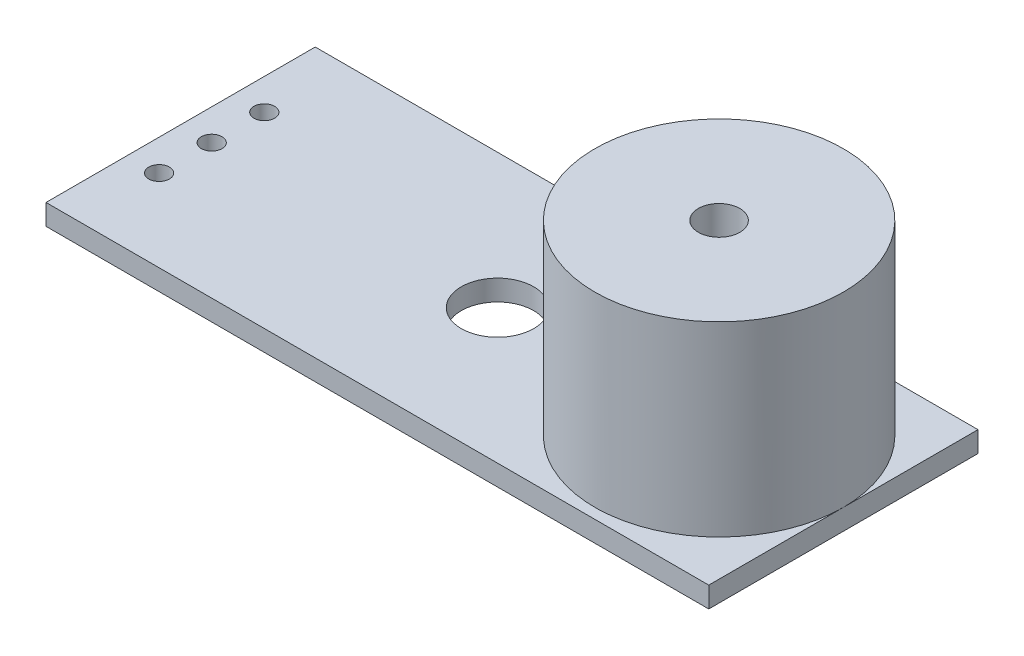
SolidWorks part; units mm, degrees
ref_plane "前视基准面" through (0, 0, 0) normal (0, 0, 1) x (1, 0, 0)
ref_plane "上视基准面" through (0, 0, 0) normal (0, 1, 0) x (1, 0, 0)
ref_plane "右视基准面" through (0, 0, 0) normal (1, 0, 0) x (0, 0, -1)
sketch "草图1" plane through (0, 0, 0) normal (0, 1, 0) x (1, 0, 0)
  line L1 (-16, 6.5) -> (16, 6.5)
  line L2 (-16, 6.5) -> (-16, -6.5)
  line L3 (-16, -6.5) -> (16, -6.5)
  line L4 (16, 6.5) -> (16, -6.5)
  line L5 (-16, 6.5) -> (16, -6.5) construction
  line L6 (-16, -6.5) -> (16, 6.5) construction
  point P0 (0, 0)
  dimension "D1" = 13
  dimension "D2" = 32
extrude "凸台-拉伸1" add sketch "草图1" along normal blind 1
sketch "草图2" plane through (0, 1, 0) normal (0, 1, 0) x (1, 0, 0)
  line L1 (16, -6.5) -> (16, 6.5) construction
  circle A0 centre (-0.7, 0) radius 1.75
  dimension "D1" = 3.5
  dimension "D2" = 16.7
extrude "切除-拉伸1" cut sketch "草图2" against normal through all
sketch "草图4" plane through (0, 1, 0) normal (0, 1, 0) x (1, 0, 0)
  line L0 (16, -6.5) -> (16, 6.5) construction
  circle A0 centre (10, 0) radius 6
  dimension "D1" = 12
extrude "凸台-拉伸2" add sketch "草图4" along normal blind 10 from surface at -1 starting at face at (-0.7, 0, 1.75)
sketch "草图5" plane through (0, 1, 0) normal (0, 1, 0) x (1, 0, 0)
  line L0 (-16, 6.5) -> (-16, -6.5) construction
  circle A0 centre (-14.5, 2.54) radius 0.5
  circle A1 centre (-14.5, 0) radius 0.5
  circle A2 centre (-14.5, -2.54) radius 0.5
  dimension "D1" = 1
  dimension "D2" = 1.5
  dimension "D3" = 3
extrude "切除-拉伸2" cut sketch "草图5" against normal through all
sketch "草图6" plane through (0, 10, 0) normal (0, 1, 0) x (1, 0, 0)
  circle A0 centre (10, 0) radius 1
  dimension "D1" = 2
extrude "切除-拉伸3" cut sketch "草图6" against normal blind 2
